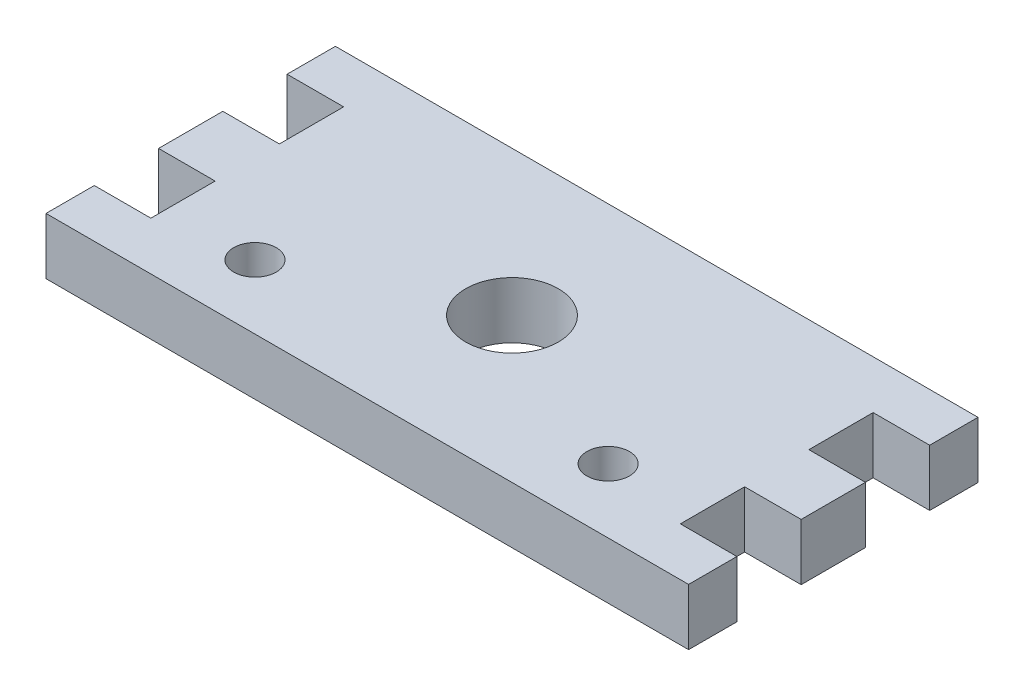
SolidWorks part; units mm, degrees
ref_plane "Front Plane" through (0, 0, 0) normal (0, 0, 1) x (1, 0, 0)
ref_plane "Top Plane" through (0, 0, 0) normal (0, 1, 0) x (1, 0, 0)
ref_plane "Right Plane" through (0, 0, 0) normal (1, 0, 0) x (0, 0, -1)
sketch "Sketch1" plane through (0, 0, 0) normal (0, 1, 0) x (1, 0, 0)
  line L0 (0, 14.3) -> (63.5, 14.3) construction
  line L1 (0, 0) -> (63.5, 0)
  line L2 (0, 0) -> (0, 4.775)
  line L3 (0, 28.6) -> (63.5, 28.6)
  line L4 (63.5, 0) -> (63.5, 4.775)
  line L5 (0, 6.35) -> (63.5, 6.35) construction
  line L6 (14.3, 6.35) -> (49.2, 6.35) construction
  line L7 (2.794, 17.475) -> (2.794, 11.125) construction
  line L8 (0, 23.825) -> (5.588, 23.825)
  line L10 (0, 17.475) -> (5.588, 17.475)
  line L11 (5.588, 23.825) -> (5.588, 17.475)
  line L12 (0, 4.775) -> (5.588, 4.775)
  line L14 (0, 11.125) -> (5.588, 11.125)
  line L15 (5.588, 4.775) -> (5.588, 11.125)
  line L16 (0, 23.825) -> (0, 28.6)
  line L17 (0, 11.125) -> (0, 17.475)
  line L18 (31.75, 28.6) -> (31.75, 0) construction
  line L19 (63.5, 4.775) -> (57.912, 4.775)
  line L20 (57.912, 4.775) -> (57.912, 11.125)
  line L21 (63.5, 11.125) -> (57.912, 11.125)
  line L22 (63.5, 17.475) -> (57.912, 17.475)
  line L23 (57.912, 23.825) -> (57.912, 17.475)
  line L24 (63.5, 23.825) -> (57.912, 23.825)
  line L25 (63.5, 23.825) -> (63.5, 28.6)
  line L26 (63.5, 11.125) -> (63.5, 17.475)
  circle A0 centre (31.75, 14.3) radius 4.575
  circle A1 centre (14.3, 6.35) radius 2.1
  circle A3 centre (49.2, 6.35) radius 2.1
  point P16 (31.75, 6.35)
  point P17 (31.75, 6.35)
  point P27 (2.794, 14.3)
  point P38 (57.5386, 14.3)
  point P39 (63.5, 14.3)
  point P40 (0, 0)
  point P41 (0, 0)
  dimension "D1" = 9.15
  dimension "D3" = 4.2
  dimension "D2" = 7.95
  dimension "D4" = 34.9
  dimension "D5" = 6.35
  dimension "D6" = 63.5
  dimension "D7" = 6.35
  dimension "D8" = 6.35
  dimension "D9" = 5.588
  dimension "D10" = 31.75
  dimension "D11" = 28.6
extrude "Boss-Extrude1" add sketch "Sketch1" along normal blind 5.588
